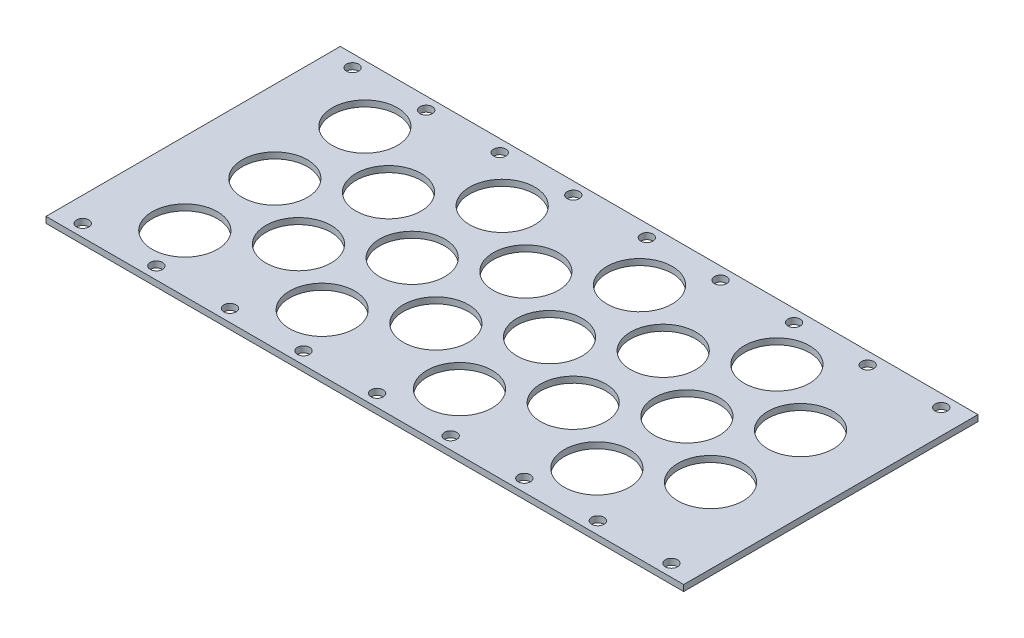
SolidWorks part; units mm, degrees
material "Plain Carbon Steel"
ref_plane "Front Plane" through (0, 0, 0) normal (0, 0, 1) x (1, 0, 0)
ref_plane "Top Plane" through (0, 0, 0) normal (0, 1, 0) x (1, 0, 0)
ref_plane "Right Plane" through (0, 0, 0) normal (1, 0, 0) x (0, 0, -1)
sketch "Sketch1" plane through (0, 0, 0) normal (0, 1, 0) x (1, 0, 0)
  line L1 (165.1, 76.2) -> (-165.1, 76.2)
  line L2 (165.1, 76.2) -> (165.1, -76.2)
  line L3 (165.1, -76.2) -> (-165.1, -76.2)
  line L4 (-165.1, 76.2) -> (-165.1, -76.2)
  line L5 (165.1, 76.2) -> (-165.1, -76.2) construction
  line L6 (165.1, -76.2) -> (-165.1, 76.2) construction
  point P0 (0, 0)
  dimension "D1" = 330.2
  dimension "D2" = 152.4
extrude "Boss-Extrude1" add sketch "Sketch1" along normal blind 3.175
sketch "Sketch2" plane through (0, 3.175, 0) normal (0, 1, 0) x (1, 0, 0)
  line L0 (165.1, 76.2) -> (-165.1, 76.2) construction
  line L1 (-165.1, 76.2) -> (-165.1, -76.2) construction
  circle A0 centre (-152.4, 69.85) radius 3.175
  circle A1 centre (-114.3, 69.85) radius 3.175
  circle A2 centre (-76.2, 69.85) radius 3.175
  circle A3 centre (-38.1, 69.85) radius 3.175
  circle A4 centre (0, 69.85) radius 3.175
  circle A5 centre (38.1, 69.85) radius 3.175
  circle A6 centre (76.2, 69.85) radius 3.175
  circle A7 centre (114.3, 69.85) radius 3.175
  circle A8 centre (152.4, 69.85) radius 3.175
  circle A9 centre (-114.3, -69.85) radius 3.175
  circle A10 centre (-76.2, -69.85) radius 3.175
  circle A11 centre (-38.1, -69.85) radius 3.175
  circle A12 centre (0, -69.85) radius 3.175
  circle A13 centre (38.1, -69.85) radius 3.175
  circle A14 centre (76.2, -69.85) radius 3.175
  circle A15 centre (114.3, -69.85) radius 3.175
  circle A16 centre (152.4, -69.85) radius 3.175
  circle A17 centre (-152.4, -69.85) radius 3.175
  dimension "D1" = 6.35
  dimension "D2" = 6.35
  dimension "D5" = 12.7
  dimension "D3" = 9
  dimension "D4" = 2
extrude "Cut-Extrude1" cut sketch "Sketch2" against normal through all
sketch "Sketch3" plane through (0, 3.175, 0) normal (0, 1, 0) x (1, 0, 0)
  line L0 (165.1, 76.2) -> (-165.1, 76.2) construction
  line L1 (-139.7, 63.5) -> (139.7, 63.5) construction
  line L2 (-139.7, 63.5) -> (-139.7, -63.5) construction
  line L3 (-139.7, -63.5) -> (139.7, -63.5) construction
  line L4 (139.7, 63.5) -> (139.7, -63.5) construction
  line L5 (-165.1, -76.2) -> (165.1, -76.2) construction
  line L6 (-165.1, 76.2) -> (-165.1, -76.2) construction
  line L7 (165.1, -76.2) -> (165.1, 76.2) construction
  line L8 (-139.7, 0) -> (139.7, 0) construction
  line L9 (-122.809, 46.609) -> (-122.809, 0) construction
  line L10 (-122.809, 23.3045) -> (-87.249, 23.3045) construction
  circle A0 centre (-122.809, 46.609) radius 16.891
  circle A1 centre (-122.809, 0) radius 16.891
  circle A2 centre (-122.809, -46.609) radius 16.891
  circle A3 centre (-87.249, 23.3045) radius 16.891
  circle A4 centre (-87.249, -23.3045) radius 16.891
  circle A5 centre (-51.689, 0) radius 16.891
  circle A6 centre (-51.689, -46.609) radius 16.891
  circle A7 centre (-16.129, -23.3045) radius 16.891
  circle A8 centre (-51.689, 46.609) radius 16.891
  circle A11 centre (-16.129, 23.3045) radius 16.891
  circle A12 centre (19.431, 0) radius 16.891
  circle A13 centre (19.431, -46.609) radius 16.891
  circle A14 centre (54.991, -23.3045) radius 16.891
  circle A15 centre (19.431, 46.609) radius 16.891
  circle A16 centre (54.991, 23.3045) radius 16.891
  circle A17 centre (90.551, 0) radius 16.891
  circle A18 centre (90.551, -46.609) radius 16.891
  circle A19 centre (126.111, -23.3045) radius 16.891
  circle A20 centre (90.551, 46.609) radius 16.891
  circle A21 centre (126.111, 23.3045) radius 16.891
  dimension "D5" = 33.782
  dimension "D6" = 35.56
  dimension "D7" = 4
  dimension "D8" = 35.56
  dimension "D9" = 71.12
  dimension "D1" = 12.7
  dimension "D2" = 12.7
  dimension "D3" = 25.4
  dimension "D4" = 25.4
extrude "Cut-Extrude2" cut sketch "Sketch3" against normal through all
